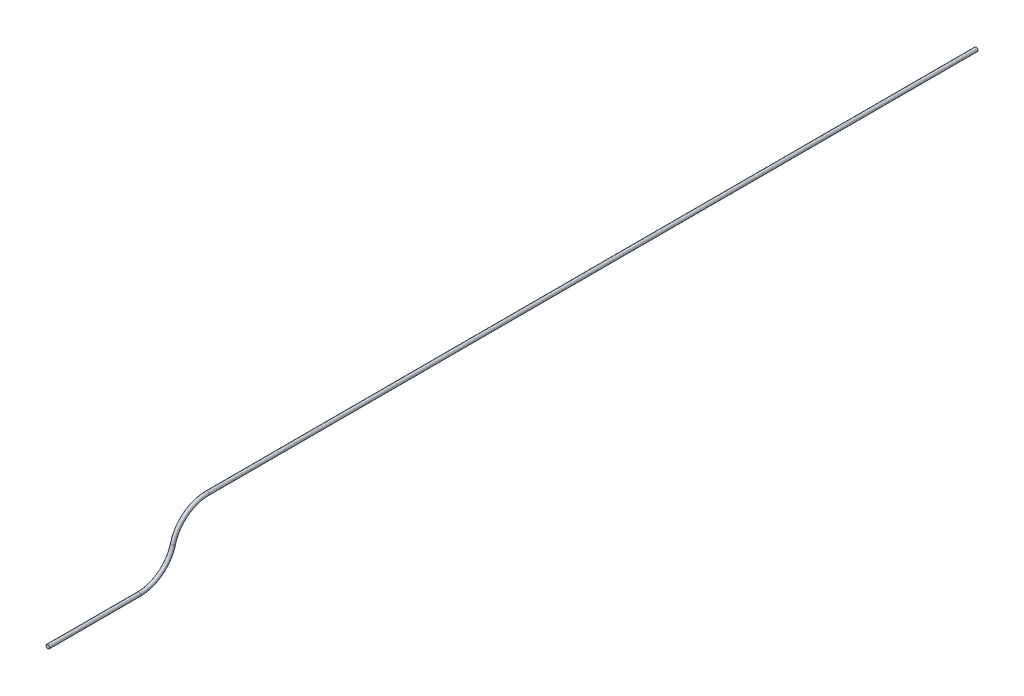
SolidWorks part; units mm, degrees
ref_plane "Front Plane" through (0, 0, 0) normal (0, 0, 1) x (1, 0, 0)
ref_plane "Top Plane" through (0, 0, 0) normal (0, 1, 0) x (1, 0, 0)
ref_plane "Right Plane" through (0, 0, 0) normal (1, 0, 0) x (0, 0, -1)
sketch "Sketch1" plane through (0, 0, 0) normal (0, 0, 1) x (1, 0, 0)
  circle A0 centre (0, 0) radius 4.0323
  dimension "D1" = 8.0645
sketch "Sketch2" plane through (0, 0, 0) normal (1, 0, 0) x (0, 0, -1)
  line L0 (0, 0) -> (195, 0)
  line L1 (342.5607, 114.3) -> (1993.5607, 114.3)
  arc A0 (195, 0) -> (268.7803, 57.15) centre (195, 76.2) ccw
  arc A1 (268.7803, 57.15) -> (342.5607, 114.3) centre (342.5607, 38.1) cw
  dimension "D3" = 76.2
  dimension "D4" = 76.2
  dimension "D1" = 195
  dimension "D2" = 114.3
  dimension "D5" = 1651
sweep "Sweep1" add profiles "Sketch1" path "Sketch2"
